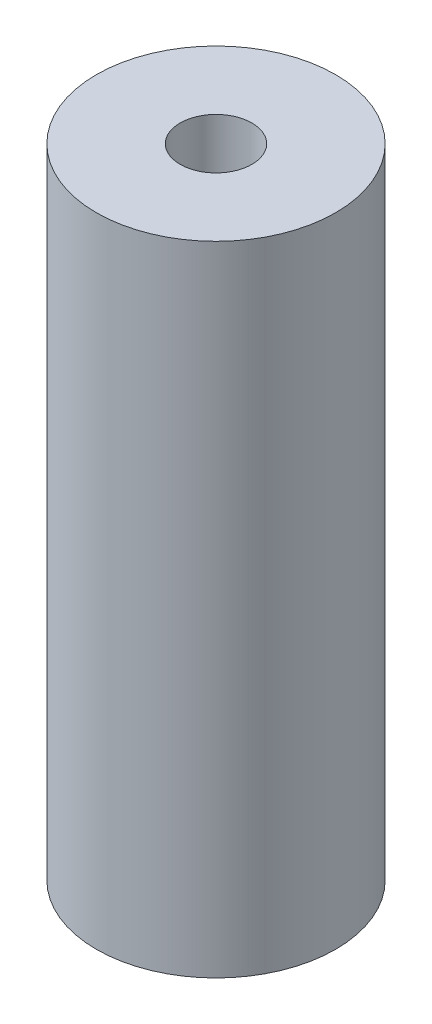
SolidWorks part; units mm, degrees
ref_plane "Front Plane" through (0, 0, 0) normal (0, 0, 1) x (1, 0, 0)
ref_plane "Top Plane" through (0, 0, 0) normal (0, 1, 0) x (1, 0, 0)
ref_plane "Right Plane" through (0, 0, 0) normal (1, 0, 0) x (0, 0, -1)
sketch "Sketch1" plane through (0, 0, 0) normal (0, 1, 0) x (1, 0, 0)
  circle A0 centre (0, 0) radius 2.25
  circle A1 centre (0, 0) radius 7.5
  dimension "D1" = 4.5
  dimension "D2" = 15
extrude "Boss-Extrude1" add sketch "Sketch1" along normal blind 40
